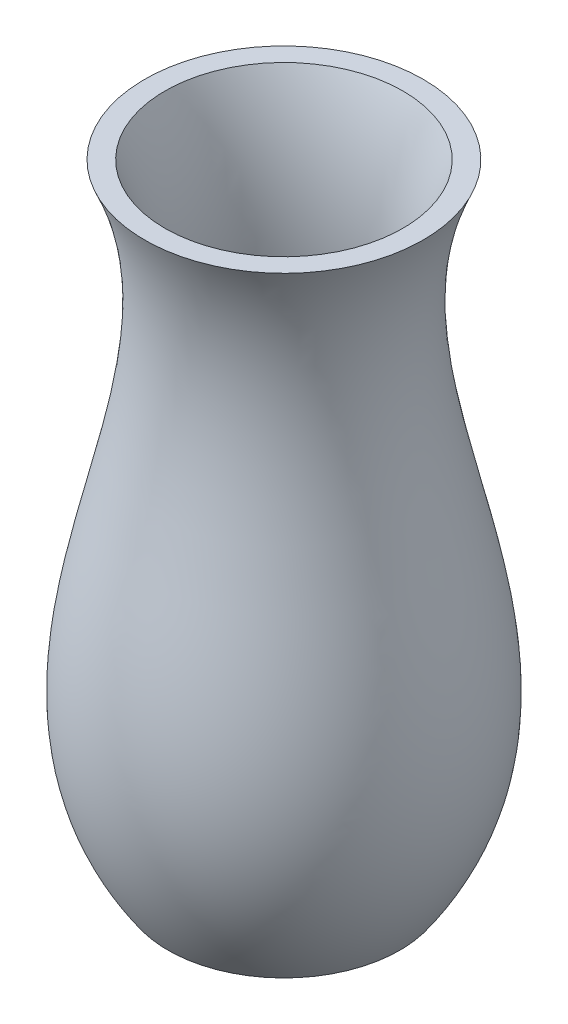
SolidWorks part; units mm, degrees
ref_plane "Front Plane" through (0, 0, 0) normal (0, 0, 1) x (1, 0, 0)
ref_plane "Top Plane" through (0, 0, 0) normal (0, 1, 0) x (1, 0, 0)
ref_plane "Right Plane" through (0, 0, 0) normal (1, 0, 0) x (0, 0, -1)
sketch "Sketch1" plane through (0, 0, 0) normal (0, 0, 1) x (1, 0, 0)
  line L0 (0, 0) -> (25, 0)
  line L1 (0, 0) -> (0, 135) construction
  line L2 (0, 50) -> (35, 50) construction
  line L3 (0, 100) -> (25, 100) construction
  line L4 (0, 135) -> (30, 135) construction
  line L5 (30, 135) -> (25.6349, 135)
  line L6 (21.7177, 2.2862) -> (0, 2.2862)
  line L7 (0, 2.2862) -> (0, 0)
  spline S0 degree 3 poles (25, 0) (56.3984, 45.0777) (9.3072, 89.3955) (30, 135) knots 0 0 0 0 1 1 1 1
  spline S1 degree 1 poles (21.7177, 2.2862) (26.3574, 136.6528) knots 0 0 1 1 construction
  spline S2 degree 3 poles (21.7177, 2.2862) (22.1741, 2.9414) (23.0718, 4.2817) (24.6989, 6.92) (26.4797, 10.2148) (28.2267, 14.1458) (30.082, 19.3752) (31.5814, 25.9064) (32.2734, 33.7979) (32.0401, 41.782) (30.7376, 52.5701) (27.7201, 66.3218) (24.204, 80.4063) (21.9623, 91.8923) (20.7953, 100.6264) (20.3792, 109.4864) (20.863, 116.9702) (21.8712, 123.0037) (22.9668, 127.5451) (24.1874, 131.3409) (25.3579, 134.3729) (26.0159, 135.9001) (26.3574, 136.6528) knots 0 0 0 0 0.015625 0.03125 0.0625 0.09375 0.125 0.1875 0.25 0.3125 0.375 0.5 0.625 0.6875 0.75 0.8125 0.875 0.90625 0.9375 0.96875 0.984375 1 1 1 1 only from (21.7177, 2.2862) to (25.6349, 135)
  dimension "D1" = 135
  dimension "D2" = 25
  dimension "D3" = 35
  dimension "D4" = 50
  dimension "D5" = 25
  dimension "D6" = 50
  dimension "D7" = 30
  dimension "D8" = 4
revolve "Revolve1" add sketch "Sketch1" angle 360 about L1
